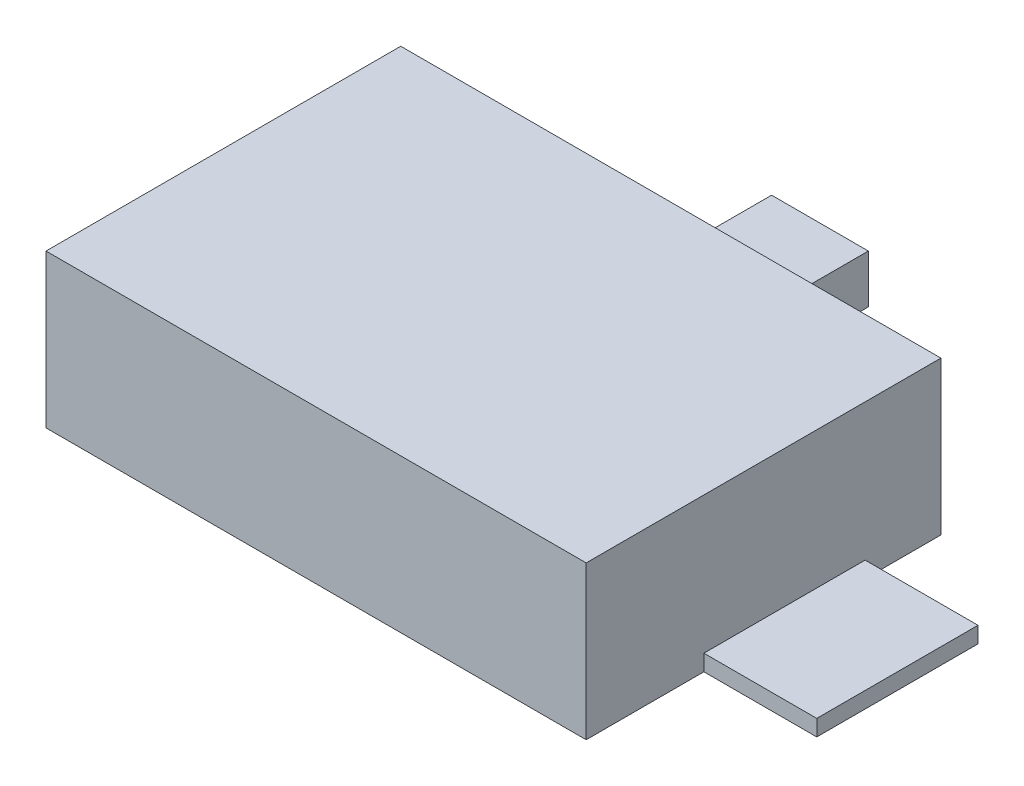
SolidWorks part; units mm, degrees
material "Delrin 2700 NC010, Low Viscosity Acetal Copolymer (SS)"
ref_plane "Front Plane" through (0, 0, 0) normal (0, 0, 1) x (1, 0, 0)
ref_plane "Top Plane" through (0, 0, 0) normal (0, 1, 0) x (1, 0, 0)
ref_plane "Right Plane" through (0, 0, 0) normal (1, 0, 0) x (0, 0, -1)
sketch "Sketch1" plane through (0, 0, 0) normal (0, 1, 0) x (1, 0, 0)
  line L0 (-42.545, 27.94) -> (42.545, -27.94) construction
  line L1 (-42.545, 27.94) -> (42.545, 27.94)
  line L2 (-42.545, 27.94) -> (-42.545, -27.94)
  line L3 (-42.545, -27.94) -> (42.545, -27.94)
  line L4 (42.545, 27.94) -> (42.545, -27.94)
  dimension "D1" = 55.88
  dimension "D2" = 85.09
extrude "Boss-Extrude1" add sketch "Sketch1" along normal blind 24.13
sketch "Sketch2" plane through (0, 0, 0) normal (0, -1, 0) x (1, 0, 0)
  line L0 (-42.545, 27.94) -> (42.545, 27.94) construction
  line L1 (60.325, 9.398) -> (42.545, 9.398)
  line L2 (60.325, 9.398) -> (60.325, -16.002)
  line L3 (60.325, -16.002) -> (42.545, -16.002)
  line L4 (42.545, 9.398) -> (42.545, -16.002)
  line L5 (42.545, 27.94) -> (42.545, -27.94) construction
  dimension "D1" = 25.4
  dimension "D2" = 17.78
  dimension "D3" = 18.542
extrude "Boss-Extrude2" add sketch "Sketch2" against normal blind 2.54
sketch "Sketch3" plane through (0, 0, -27.94) normal (0, 0, -1) x (-1, 0, 0)
  line L0 (-42.545, 0) -> (42.545, 0) construction
  line L1 (9.525, 7.62) -> (-5.715, 7.62)
  line L2 (9.525, 7.62) -> (9.525, 0)
  line L3 (9.525, 0) -> (-5.715, 0)
  line L4 (-5.715, 7.62) -> (-5.715, 0)
  line L5 (-42.545, 24.13) -> (-42.545, 0) construction
  dimension "D1" = 7.62
  dimension "D2" = 15.24
  dimension "D3" = 36.83
extrude "Boss-Extrude3" add sketch "Sketch3" along normal blind 25.4
